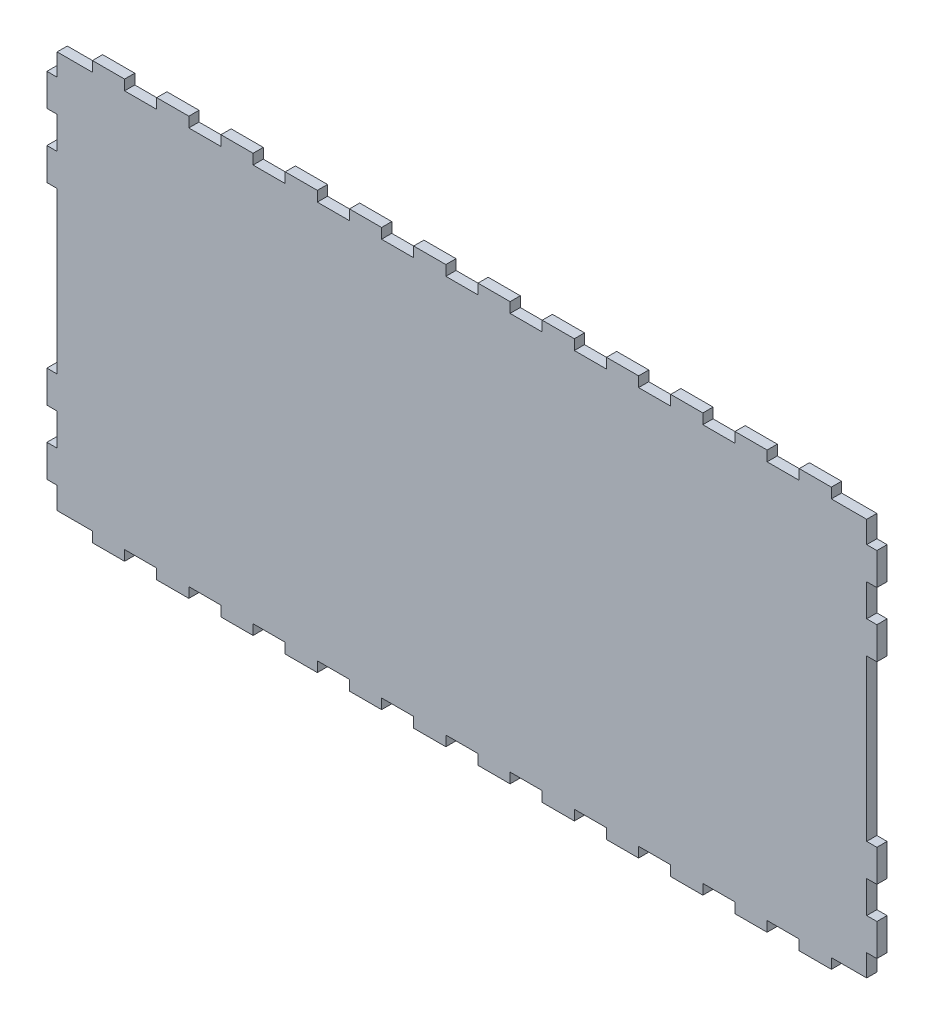
SolidWorks part; units mm, degrees
ref_plane "Front Plane" through (0, 0, 0) normal (0, 0, 1) x (1, 0, 0)
ref_plane "Top Plane" through (0, 0, 0) normal (0, 1, 0) x (1, 0, 0)
ref_plane "Right Plane" through (0, 0, 0) normal (1, 0, 0) x (0, 0, -1)
sketch "Sketch1" plane through (0, 0, 0) normal (0, 0, 1) x (1, 0, 0)
  line L0 (31, 123.65) -> (31, 126.825)
  line L1 (31, 0) -> (31, -3.175)
  line L2 (0, 0) -> (0, 123.65) construction
  line L3 (31, 126.825) -> (41, 126.825)
  line L4 (252, 123.65) -> (0, 0) construction
  line L5 (41, 123.65) -> (41, 126.825)
  line L6 (11, 123.65) -> (11, 126.825)
  line L7 (11, 126.825) -> (21, 126.825)
  line L8 (21, 123.65) -> (21, 126.825)
  line L9 (51, 123.65) -> (51, 126.825)
  line L10 (51, 126.825) -> (61, 126.825)
  line L11 (61, 123.65) -> (61, 126.825)
  line L12 (71, 123.65) -> (71, 126.825)
  line L13 (71, 126.825) -> (81, 126.825)
  line L14 (81, 123.65) -> (81, 126.825)
  line L15 (91, 123.65) -> (91, 126.825)
  line L16 (91, 126.825) -> (101, 126.825)
  line L17 (101, 123.65) -> (101, 126.825)
  line L18 (111, 123.65) -> (111, 126.825)
  line L19 (111, 126.825) -> (121, 126.825)
  line L20 (121, 123.65) -> (121, 126.825)
  line L21 (131, 123.65) -> (131, 126.825)
  line L22 (131, 126.825) -> (141, 126.825)
  line L23 (141, 123.65) -> (141, 126.825)
  line L24 (151, 123.65) -> (151, 126.825)
  line L25 (151, 126.825) -> (161, 126.825)
  line L26 (161, 123.65) -> (161, 126.825)
  line L27 (171, 123.65) -> (171, 126.825)
  line L28 (171, 126.825) -> (181, 126.825)
  line L29 (181, 123.65) -> (181, 126.825)
  line L30 (191, 123.65) -> (191, 126.825)
  line L31 (191, 126.825) -> (201, 126.825)
  line L32 (201, 123.65) -> (201, 126.825)
  line L33 (211, 123.65) -> (211, 126.825)
  line L34 (211, 126.825) -> (221, 126.825)
  line L35 (221, 123.65) -> (221, 126.825)
  line L36 (231, 123.65) -> (231, 126.825)
  line L37 (231, 126.825) -> (241, 126.825)
  line L38 (241, 123.65) -> (241, 126.825)
  line L39 (11, 123.65) -> (31, 123.65) construction
  line L40 (11, 123.65) -> (0, 123.65)
  line L41 (21, 123.65) -> (31, 123.65)
  line L42 (41, 123.65) -> (51, 123.65)
  line L43 (61, 123.65) -> (71, 123.65)
  line L44 (81, 123.65) -> (91, 123.65)
  line L45 (101, 123.65) -> (111, 123.65)
  line L46 (121, 123.65) -> (131, 123.65)
  line L47 (141, 123.65) -> (151, 123.65)
  line L48 (161, 123.65) -> (171, 123.65)
  line L49 (181, 123.65) -> (191, 123.65)
  line L50 (201, 123.65) -> (211, 123.65)
  line L51 (221, 123.65) -> (231, 123.65)
  line L52 (241, 123.65) -> (252, 123.65)
  line L53 (0, 123.65) -> (252.0269, -0.0172) construction
  line L54 (31, -3.175) -> (41, -3.175)
  line L55 (41, 0) -> (41, -3.175)
  line L56 (11, 0) -> (11, -3.175)
  line L57 (11, -3.175) -> (21, -3.175)
  line L58 (21, 0) -> (21, -3.175)
  line L59 (51, 0) -> (51, -3.175)
  line L60 (51, -3.175) -> (61, -3.175)
  line L61 (61, 0) -> (61, -3.175)
  line L62 (71, 0) -> (71, -3.175)
  line L63 (71, -3.175) -> (81, -3.175)
  line L64 (81, 0) -> (81, -3.175)
  line L65 (91, 0) -> (91, -3.175)
  line L66 (91, -3.175) -> (101, -3.175)
  line L67 (101, 0) -> (101, -3.175)
  line L68 (111, 0) -> (111, -3.175)
  line L69 (111, -3.175) -> (121, -3.175)
  line L70 (121, 0) -> (121, -3.175)
  line L71 (131, 0) -> (131, -3.175)
  line L72 (131, -3.175) -> (141, -3.175)
  line L73 (141, 0) -> (141, -3.175)
  line L74 (151, 0) -> (151, -3.175)
  line L75 (151, -3.175) -> (161, -3.175)
  line L76 (161, 0) -> (161, -3.175)
  line L77 (171, 0) -> (171, -3.175)
  line L78 (171, -3.175) -> (181, -3.175)
  line L79 (181, 0) -> (181, -3.175)
  line L80 (191, 0) -> (191, -3.175)
  line L81 (191, -3.175) -> (201, -3.175)
  line L82 (201, 0) -> (201, -3.175)
  line L83 (211, 0) -> (211, -3.175)
  line L84 (211, -3.175) -> (221, -3.175)
  line L85 (221, 0) -> (221, -3.175)
  line L86 (231, 0) -> (231, -3.175)
  line L87 (231, -3.175) -> (241, -3.175)
  line L88 (241, 0) -> (241, -3.175)
  line L89 (11, 0) -> (31, 0) construction
  line L90 (11, 0) -> (0, 0)
  line L91 (21, 0) -> (31, 0)
  line L92 (41, 0) -> (51, 0)
  line L93 (61, 0) -> (71, 0)
  line L94 (81, 0) -> (91, 0)
  line L95 (101, 0) -> (111, 0)
  line L96 (121, 0) -> (131, 0)
  line L97 (141, 0) -> (151, 0)
  line L98 (161, 0) -> (171, 0)
  line L99 (181, 0) -> (191, 0)
  line L100 (201, 0) -> (211, 0)
  line L101 (221, 0) -> (231, 0)
  line L102 (241, 0) -> (252, 0)
  line L103 (252, 0) -> (252.0269, -0.0172)
  line L104 (0, 123.65) -> (0, 116.825)
  line L105 (0, 116.825) -> (-3.175, 116.825)
  line L106 (0, 106.825) -> (0, 96.825)
  line L107 (0, 106.825) -> (-3.175, 106.825)
  line L108 (-3.175, 116.825) -> (-3.175, 106.825)
  line L109 (0, 86.825) -> (0, 36.825)
  line L110 (0, 96.825) -> (-3.175, 96.825)
  line L111 (0, 0) -> (0, 6.825)
  line L112 (0, 86.825) -> (-3.175, 86.825)
  line L113 (-3.175, 96.825) -> (-3.175, 86.825)
  line L114 (-3.175, 26.825) -> (-3.175, 36.825)
  line L115 (0, 36.825) -> (-3.175, 36.825)
  line L116 (0, 26.825) -> (-3.175, 26.825)
  line L117 (-3.175, 6.825) -> (-3.175, 16.825)
  line L118 (0, 16.825) -> (-3.175, 16.825)
  line L119 (0, 16.825) -> (0, 26.825)
  line L120 (0, 6.825) -> (-3.175, 6.825)
  line L121 (126, 61.825) -> (126, 101.4972) construction
  line L122 (252, 0) -> (252, 6.825)
  line L123 (252, 6.825) -> (255.175, 6.825)
  line L124 (252, 16.825) -> (252, 26.825)
  line L125 (252, 16.825) -> (255.175, 16.825)
  line L126 (255.175, 6.825) -> (255.175, 16.825)
  line L127 (252, 26.825) -> (255.175, 26.825)
  line L128 (252, 36.825) -> (255.175, 36.825)
  line L129 (255.175, 26.825) -> (255.175, 36.825)
  line L130 (255.175, 96.825) -> (255.175, 86.825)
  line L131 (252, 86.825) -> (255.175, 86.825)
  line L132 (252, 96.825) -> (255.175, 96.825)
  line L133 (252, 86.825) -> (252, 36.825)
  line L134 (255.175, 116.825) -> (255.175, 106.825)
  line L135 (252, 106.825) -> (255.175, 106.825)
  line L136 (252, 106.825) -> (252, 96.825)
  line L137 (252, 116.825) -> (255.175, 116.825)
  line L138 (252, 123.65) -> (252, 116.825)
  line L144 (0, 0) -> (252, 0) construction
  point P118 (0, 61.825)
  point P143 (252, 61.825)
  dimension "D1" = 123.65
  dimension "D3" = 10
  dimension "D4" = 3.175
  dimension "D5" = 11
  dimension "D7" = 20
  dimension "D8" = 11
  dimension "D9" = 3.175
  dimension "D10" = 6.825
  dimension "D11" = 10
  dimension "D13" = 20
  dimension "D14" = 11
  dimension "D15" = 10
  dimension "D16" = 3.175
  dimension "D17" = 10
  dimension "D18" = 10
  dimension "D19" = 10
  dimension "D20" = 3.175
  dimension "D21" = 10
  dimension "D22" = 10
  dimension "D23" = 3.175
  dimension "D24" = 10
  dimension "D6" = 12
  dimension "D12" = 12
extrude "Boss-Extrude1" add sketch "Sketch1" along normal blind 3.175 contours L138 L52 L38 L37 L36 L51 L35 L34 L33 L50 L32 L31 L30 L49 L29 L28 L27 L48 L26 L25 L24 L47 L23 L22 L21 L46 L20 L19 L18 L45 L17 L16 L15 L44 L14 L13 L12 L43 L11 L10 L9 L42 L5 L3 L0 L41 L8 L7 L6 L40 L104
